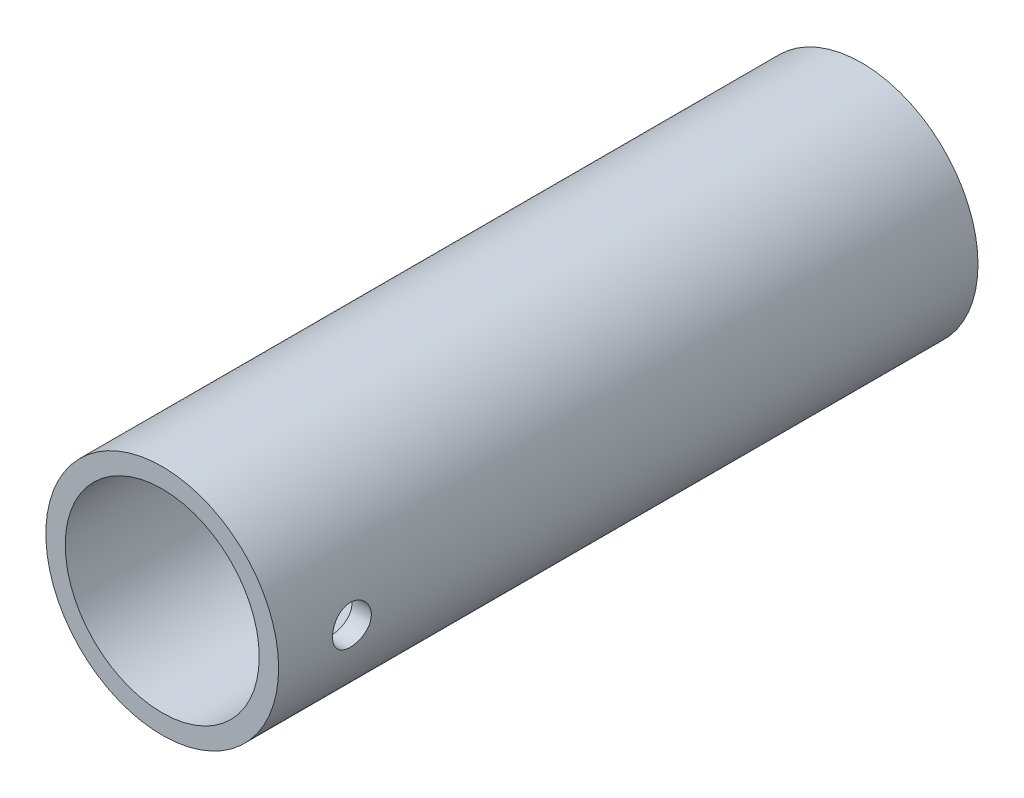
SolidWorks part; units mm, degrees
material "Delrin 2700 NC010, Low Viscosity Acetal Copolymer (SS)"
ref_plane "Front Plane" through (0, 0, 0) normal (0, 0, 1) x (1, 0, 0)
ref_plane "Top Plane" through (0, 0, 0) normal (0, 1, 0) x (1, 0, 0)
ref_plane "Right Plane" through (0, 0, 0) normal (1, 0, 0) x (0, 0, -1)
sketch "Sketch1" plane through (0, 0, 0) normal (0, 0, 1) x (1, 0, 0)
  circle A0 centre (0, 0) radius 9.525
  circle A1 centre (0, 0) radius 7.9375
  dimension "D1" = 19.05
  dimension "D2" = 15.875
extrude "Boss-Extrude1" add sketch "Sketch1" along normal blind 57.24
ref_plane "Plane1" through (9.525, 0, 0) normal (1, 0, 0) x (0, 0, -1)
sketch "Sketch2" plane through (9.525, 0, 0) normal (1, 0, 0) x (0, 0, -1)
  line L0 (-57.24, 9.525) -> (-57.24, -9.525) construction
  circle A0 centre (-51.24, 0) radius 1.5875
  point P5 (-57.24, 0)
  dimension "D2" = 3.175
  dimension "D1" = 6
extrude "Cut-Extrude1" cut sketch "Sketch2" against normal up to next
ref_plane "Plane2" through (-9.525, 0, 0) normal (-1, 0, 0) x (0, 0, 1)
sketch "Sketch3" plane through (-9.525, 0, 0) normal (-1, 0, 0) x (0, 0, 1)
  line L0 (0, 9.525) -> (0, -9.525) construction
  line L1 (13, -7) -> (40.24, -7)
  line L2 (13, -7) -> (13, 6.5)
  line L5 (13, 6.5) -> (40.24, 6.5)
  line L6 (40.24, -7) -> (40.24, 6.5)
  line L7 (13, -7) -> (40.24, 6.5) construction
  line L8 (13, 6.5) -> (40.24, -7) construction
  line L9 (57.24, -9.525) -> (57.24, 9.525) construction
  line L10 (0, 0) -> (57.24, 0) construction
  point P0 (26.62, -0.25)
  dimension "D3" = 7
  dimension "D1" = 13
  dimension "D2" = 17
  dimension "D4" = 6.5
extrude "Cut-Extrude2" cut sketch "Sketch3" against normal up to next
equation "\"D1@Boss-Extrude1\"=1.08*53.00mm"
